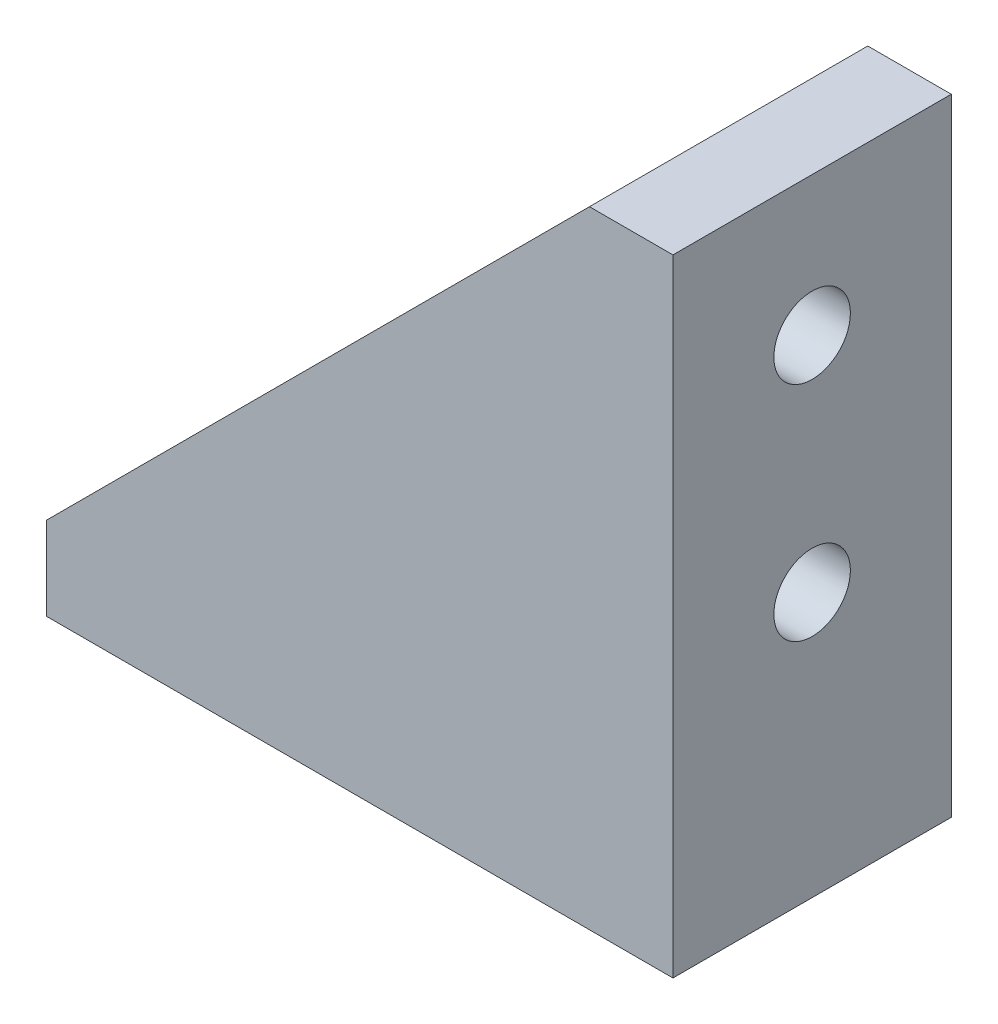
SolidWorks part; units mm, degrees
ref_plane "Alzado" through (0, 0, 0) normal (0, 0, 1) x (1, 0, 0)
ref_plane "Planta" through (0, 0, 0) normal (0, 1, 0) x (1, 0, 0)
ref_plane "Vista lateral" through (0, 0, 0) normal (1, 0, 0) x (0, 0, -1)
sketch "Croquis1" plane through (0, 0, 0) normal (0, 0, 1) x (1, 0, 0)
  line L0 (0, 0) -> (45, 0)
  line L1 (45, 0) -> (45, 45)
  line L2 (45, 45) -> (39, 45)
  line L3 (39, 45) -> (0, 6)
  line L4 (0, 6) -> (0, 0)
  dimension "D1" = 6
  dimension "D2" = 6
  dimension "D3" = 45
  dimension "D4" = 45
extrude "Saliente-Extruir1" add sketch "Croquis1" along normal blind 20
sketch "Croquis2" plane through (0, 0, 0) normal (-1, 0, 0) x (0, 0, 1)
  line L0 (20, 6) -> (0, 6) construction
  line L1 (16, 45) -> (4, 45)
  line L2 (16, 45) -> (16, 6)
  line L3 (16, 6) -> (4, 6)
  line L4 (4, 45) -> (4, 6)
  line L5 (0, 45) -> (0, 6) construction
  line L6 (20, 45) -> (20, 6) construction
  line L7 (20, 45) -> (0, 45) construction
  point P12 (0, 0)
  dimension "D1" = 4
  dimension "D2" = 4
  dimension "D3" = 0
extrude "Cortar-Extruir1" cut sketch "Croquis2" against normal up to vertex (39 mm away)
sketch "Croquis3" plane through (45, 0, 0) normal (1, 0, 0) x (0, 0, -1)
  line L0 (-20, 45) -> (0, 45) construction
  line L2 (0, 0) -> (0, 45) construction
  circle A0 centre (-10, 35) radius 2.75
  circle A1 centre (-10, 19) radius 2.75
  point P8 (-60.8706, 35.4139)
  dimension "D1" = 5.5
  dimension "D2" = 5.5
  dimension "D3" = 16
  dimension "D4" = 10
  dimension "D5" = 10
  dimension "D6" = 10
extrude "Cortar-Extruir2" cut sketch "Croquis3" against normal up to next
sketch "Croquis4" plane through (0, 0, 0) normal (0, -1, 0) x (1, 0, 0)
  line L1 (0, 20) -> (45, 20) construction
  line L2 (0, 20) -> (0, 0) construction
  circle A0 centre (10, 10) radius 2.75
  circle A1 centre (26, 10) radius 2.75
  point P6 (33.3428, 12.0572)
  dimension "D1" = 5.5
  dimension "D2" = 5.5
  dimension "D3" = 16
  dimension "D4" = 10
  dimension "D5" = 10
  dimension "D6" = 10
extrude "Cortar-Extruir3" cut sketch "Croquis4" against normal up to next
